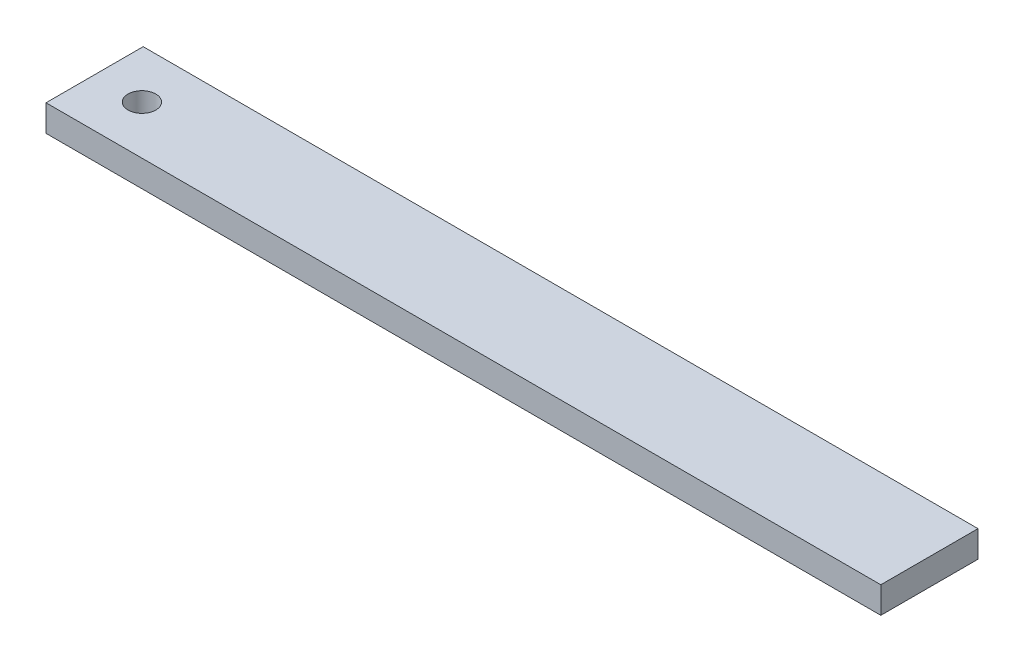
SolidWorks part; units mm, degrees
ref_plane "Front Plane" through (0, 0, 0) normal (0, 0, 1) x (1, 0, 0)
ref_plane "Top Plane" through (0, 0, 0) normal (0, 1, 0) x (1, 0, 0)
ref_plane "Right Plane" through (0, 0, 0) normal (1, 0, 0) x (0, 0, -1)
sketch "Sketch1" plane through (0, 0, 0) normal (0, 1, 0) x (1, 0, 0)
  line L0 (-300, 17.4625) -> (-283, 17.4625) construction
  line L1 (0, 0) -> (-300, 0)
  line L2 (0, 0) -> (0, 34.925)
  line L3 (0, 34.925) -> (-300, 34.925)
  line L4 (-300, 0) -> (-300, 34.925)
  circle A0 centre (-283, 17.4625) radius 5
  dimension "D3" = 17
  dimension "D1" = 300
  dimension "D2" = 34.925
extrude "Boss-Extrude1" add sketch "Sketch1" along normal blind 9.525
